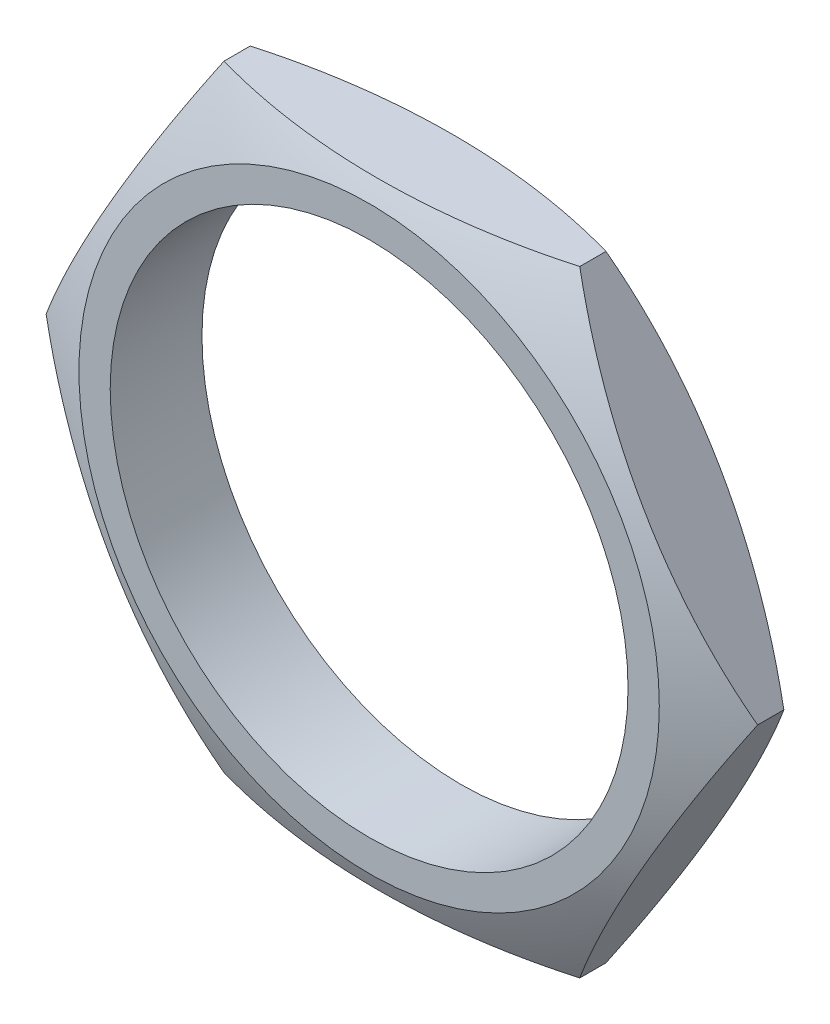
SolidWorks part; units mm, degrees
ref_plane "Plan de face" through (0, 0, 0) normal (0, 0, 1) x (1, 0, 0)
ref_plane "Plan de dessus" through (0, 0, 0) normal (0, 1, 0) x (1, 0, 0)
ref_plane "Plan de droite" through (0, 0, 0) normal (1, 0, 0) x (0, 0, -1)
sketch "Esquisse1" plane through (0, 0, 0) normal (0, 0, 1) x (1, 0, 0)
  line L1 (10.8542, 0) -> (5.4271, 9.4)
  line L2 (5.4271, 9.4) -> (-5.4271, 9.4)
  line L3 (-5.4271, 9.4) -> (-10.8542, 0)
  line L4 (-10.8542, 0) -> (-5.4271, -9.4)
  line L5 (-5.4271, -9.4) -> (5.4271, -9.4)
  line L6 (5.4271, -9.4) -> (10.8542, 0)
  circle A0 centre (0, 0) radius 7.9
  circle A1 centre (0, 0) radius 9.4 construction
  dimension "D2" = 15.8
  dimension "D1" = 18.8
extrude "Boss.-Extru.1" add sketch "Esquisse1" along normal mid plane 2.8
sketch "Esquisse2" plane through (0, 0, 0) normal (0, 1, 0) x (1, 0, 0)
  line L1 (-10.8542, -1.4) -> (-10.8542, 1.4) construction
  line L2 (10.8542, -1.4) -> (10.8542, 1.4) construction
  line L3 (-5.4271, 1.4) -> (-10.8542, 1.4) construction
  line L4 (0, 0) -> (0, 7.365) construction
  line L5 (-10.8542, 0.4) -> (-10.8542, 1.4)
  line L6 (-10.8542, 1.4) -> (10.8542, 1.4)
  line L7 (10.8542, 1.4) -> (10.8542, 0.4)
  arc A0 (-10.8542, 0.4) -> (10.8542, 0.4) centre (0, -18.8084) cw
  point P7 (-8.8542, 1.4)
  dimension "D1" = 1
  dimension "D2" = 2
revolve "Enlèvement de matière-Révolution1" cut sketch "Esquisse2" angle 360 about L4
mirror "Symétrie1" about plane through (0, 0, 0) normal (0, 0, 1) of "Enlèvement de matière-Révolution1"
